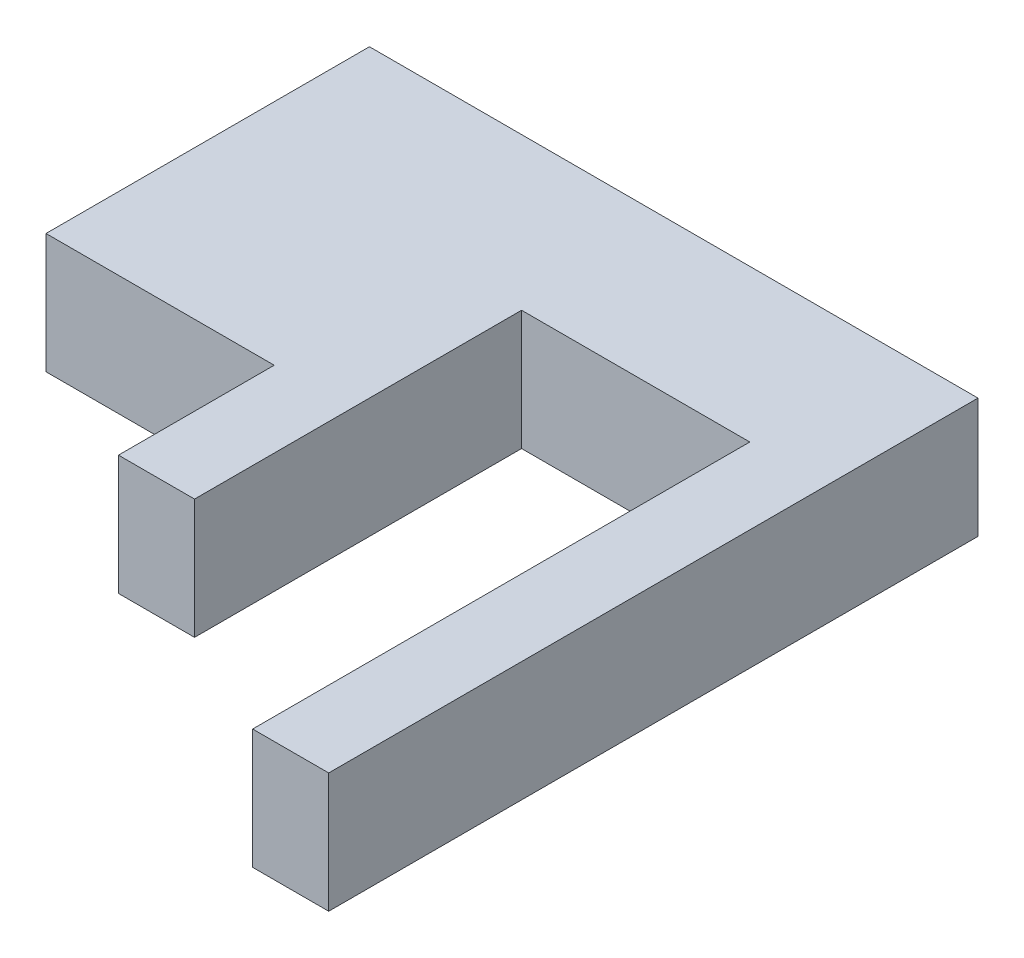
SolidWorks part; units mm, degrees
ref_plane "Front Plane" through (0, 0, 0) normal (0, 0, 1) x (1, 0, 0)
ref_plane "Top Plane" through (0, 0, 0) normal (0, 1, 0) x (1, 0, 0)
ref_plane "Right Plane" through (0, 0, 0) normal (1, 0, 0) x (0, 0, -1)
sketch "Sketch1" plane through (0, 0, 0) normal (0, 1, 0) x (1, 0, 0)
  line L1 (-111.211, 33.6246) -> (-85.811, 33.6246)
  line L2 (-111.211, 33.6246) -> (-111.211, 6.6246)
  line L3 (-92.161, -6.3754) -> (-85.811, -6.3754)
  line L4 (-85.811, 20.9246) -> (-85.811, -6.3754)
  line L5 (-85.811, 33.6246) -> (-60.411, 33.6246)
  line L7 (-85.811, 20.9246) -> (-66.761, 20.9246)
  line L8 (-60.411, 33.6246) -> (-60.411, 31.8869)
  line L10 (-66.761, 20.9246) -> (-66.761, -20.5754)
  line L11 (-66.761, -20.5754) -> (-60.411, -20.5754)
  line L12 (-60.411, 31.8869) -> (-60.411, -20.5754)
  line L13 (-111.211, 6.6246) -> (-92.161, 6.6246)
  line L14 (-92.161, -6.3754) -> (-92.161, 6.6246)
  dimension "D1" = 40
  dimension "D2" = 25.4
  dimension "D3" = 6.35
  dimension "D4" = 44.45
  dimension "D5" = 12.7
  dimension "D7" = 13
  dimension "D8" = 6.35
extrude "Boss-Extrude1" add sketch "Sketch1" along normal blind 10
